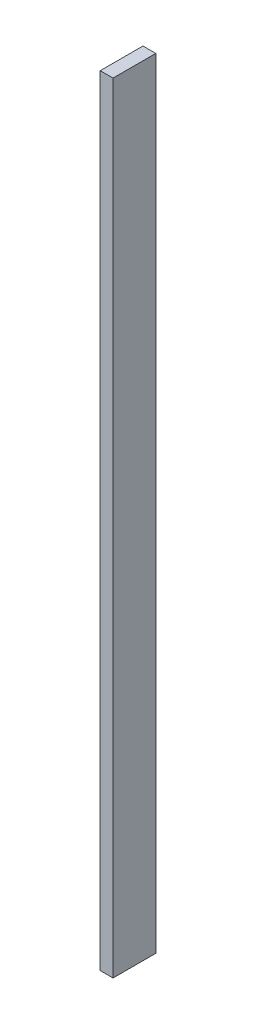
SolidWorks part; units mm, degrees
material "1023 Kohlenstoffstahlblech (SS)"
ref_plane "Ebene vorne" through (0, 0, 0) normal (0, 0, 1) x (1, 0, 0)
ref_plane "Ebene oben" through (0, 0, 0) normal (0, 1, 0) x (1, 0, 0)
ref_plane "Ebene rechts" through (0, 0, 0) normal (1, 0, 0) x (0, 0, -1)
sketch "Skizze1" plane through (0, 0, 0) normal (0, 1, 0) x (1, 0, 0)
  line L1 (-1.5, -5) -> (1.5, -5)
  line L2 (-1.5, -5) -> (-1.5, 5)
  line L3 (-1.5, 5) -> (1.5, 5)
  line L4 (1.5, -5) -> (1.5, 5)
  line L5 (-1.5, -5) -> (1.5, 5) construction
  line L6 (-1.5, 5) -> (1.5, -5) construction
  line L7 (-4, -13.3333) -> (4, -13.3333) construction
  line L8 (-4, -13.3333) -> (-4, 13.3333) construction
  line L9 (-4, 13.3333) -> (4, 13.3333) construction
  line L10 (4, -13.3333) -> (4, 13.3333) construction
  line L11 (-4, -13.3333) -> (4, 13.3333) construction
  line L12 (-4, 13.3333) -> (4, -13.3333) construction
  point P0 (0, 0)
  point P5 (0, 0)
  dimension "D1" = 10
  dimension "D2" = 8
  dimension "D3" = 3
extrude "Aufsatz-Linear austragen1" add sketch "Skizze1" along normal blind 182.4
